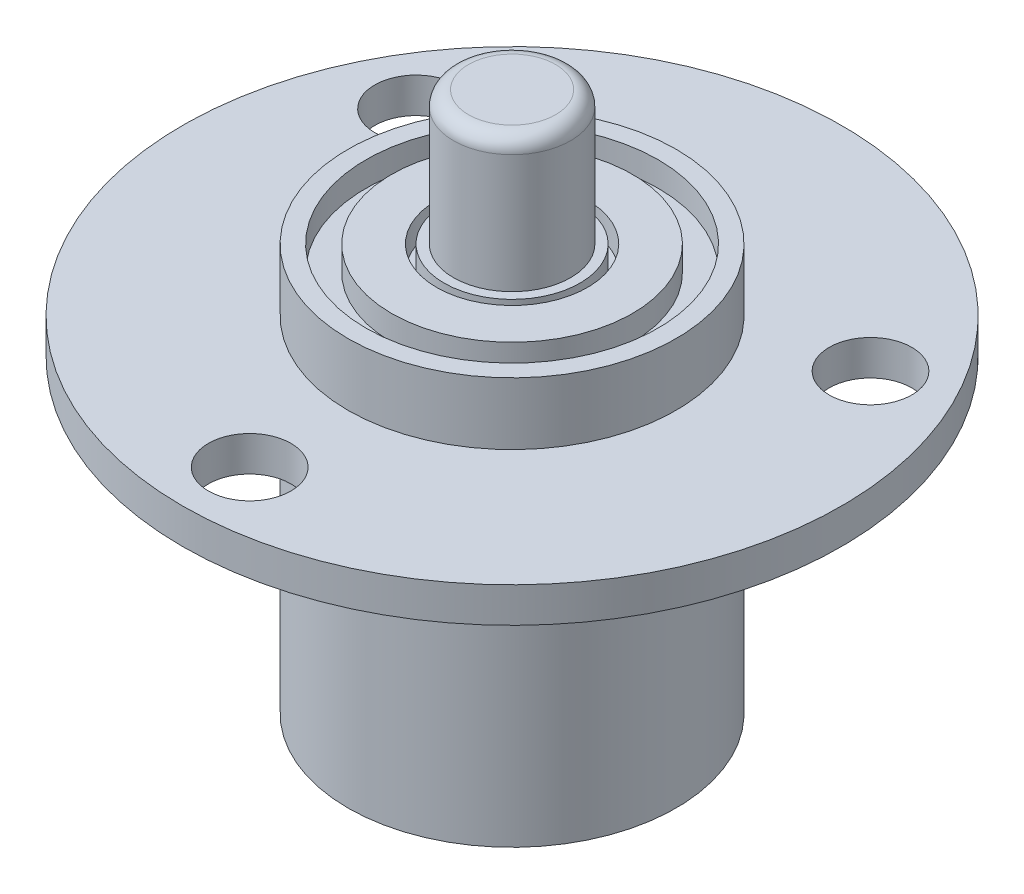
SolidWorks part; units mm, degrees
ref_plane "Front Plane" through (0, 0, 0) normal (0, 0, 1) x (1, 0, 0)
ref_plane "Top Plane" through (0, 0, 0) normal (0, 1, 0) x (1, 0, 0)
ref_plane "Right Plane" through (0, 0, 0) normal (1, 0, 0) x (0, 0, -1)
sketch "Sketch1" plane through (0, 0, 0) normal (0, 1, 0) x (1, 0, 0)
  circle A0 centre (0, 0) radius 21.95
  dimension "D1" = 43.9
extrude "Boss-Extrude1" add sketch "Sketch1" along normal blind 2.34
sketch "Sketch2" plane through (0, 2.34, 0) normal (0, 1, 0) x (1, 0, 0)
  circle A0 centre (0, 0) radius 10.925
  dimension "D1" = 21.85
extrude "Boss-Extrude2" add sketch "Sketch2" along normal blind 4.14 and the other way offset from surface (22.94 mm away) 20.6 contours A0 other way up to face at (0, 0, 21.95)
sketch "Sketch3" plane through (0, 0, 0) normal (0, -1, 0) x (1, 0, 0)
  line L0 (0, 14.725) -> (0, 10.925) construction
  circle A0 centre (0, 17.475) radius 2.75
  circle A1 centre (0, 0) radius 10.925 construction
  dimension "D1" = 5.5
  dimension "D2" = 3.8
extrude "Cut-Extrude1" cut sketch "Sketch3" against normal through all
pattern_circular "CirPattern1" count 3 over 360 about axis through (0, 0, 0) along (0, 1, 0) of "Cut-Extrude1"
sketch "Sketch4" plane through (0, 6.48, 0) normal (0, 1, 0) x (1, 0, 0)
  circle A0 centre (0, 0) radius 9.725
  circle A1 centre (0, 0) radius 8.025
  circle A2 centre (0, 0) radius 10.925 construction
  circle A3 centre (0, 0) radius 5.025
  circle A4 centre (0, 0) radius 4.525
  dimension "D1" = 1.2
  dimension "D2" = 3
  dimension "D3" = 1.7
  dimension "D4" = 0.5
extrude "Cut-Extrude2" cut sketch "Sketch4" against normal blind 1.65 contours A0 A1 | A3 A4
sketch "Sketch5" plane through (0, 6.48, 0) normal (0, 1, 0) x (1, 0, 0)
  circle A0 centre (0, 0) radius 3.9
  dimension "D1" = 7.8
extrude "Boss-Extrude3" add sketch "Sketch5" along normal blind 8.9 contours A0
fillet "Fillet1" radius 1 1 edges at (0, 15.38, 3.9)
